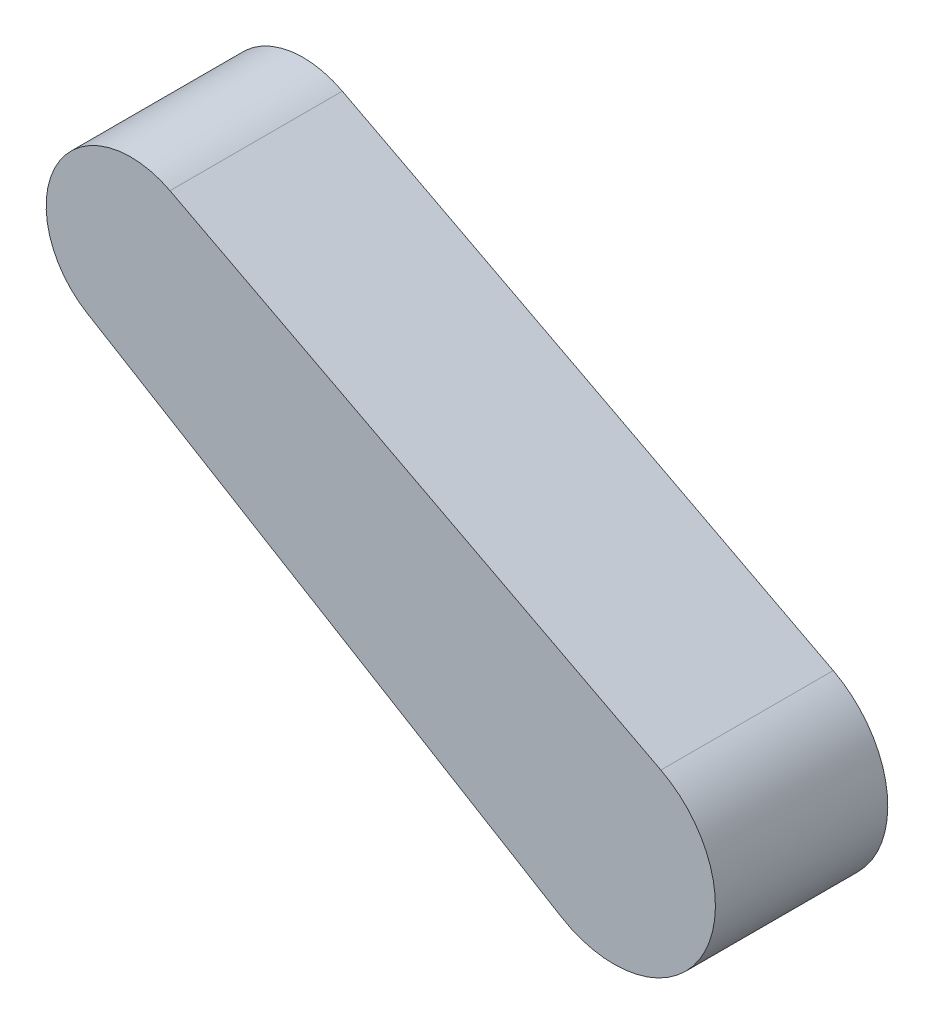
SolidWorks part; units mm, degrees
ref_plane "Front" through (0, 0, 0) normal (0, 0, 1) x (1, 0, 0)
ref_plane "Top" through (0, 0, 0) normal (0, 1, 0) x (1, 0, 0)
ref_plane "Right" through (0, 0, 0) normal (1, 0, 0) x (0, 0, -1)
sketch "Sketch1" plane through (0, 0, 0) normal (0, 0, 1) x (1, 0, 0)
  line L0 (-1108.9696, 252.4) -> (-1507.5901, 476.3053) construction
  line L1 (-1108.9696, 252.4) -> (-1507.5901, 476.3053)
  line L2 (-1543.6427, 416.4786) -> (-1152.2328, 180.608)
  line L3 (-1475.2592, 538.2224) -> (-1070.1725, 326.7006)
  arc A0 (-1070.1725, 326.7006) -> (-1152.2328, 180.608) centre (-1108.9696, 252.4) cw
  arc A1 (-1475.2592, 538.2224) -> (-1543.6427, 416.4786) centre (-1507.5901, 476.3053) ccw
  dimension "D1" = 69.85
  dimension "D2" = 83.82
extrude "Boss-Extrude1" add sketch "Sketch1" against normal blind 142.24
equation "\"mass\"= \"human weight@FS2-FR-HA-A-0001-V1, HUMAN ANALOG.Assembly\" * \"thigh percent@FS2-FR-HA-A-0001-V1, HUMAN ANALOG.Assembly\""
